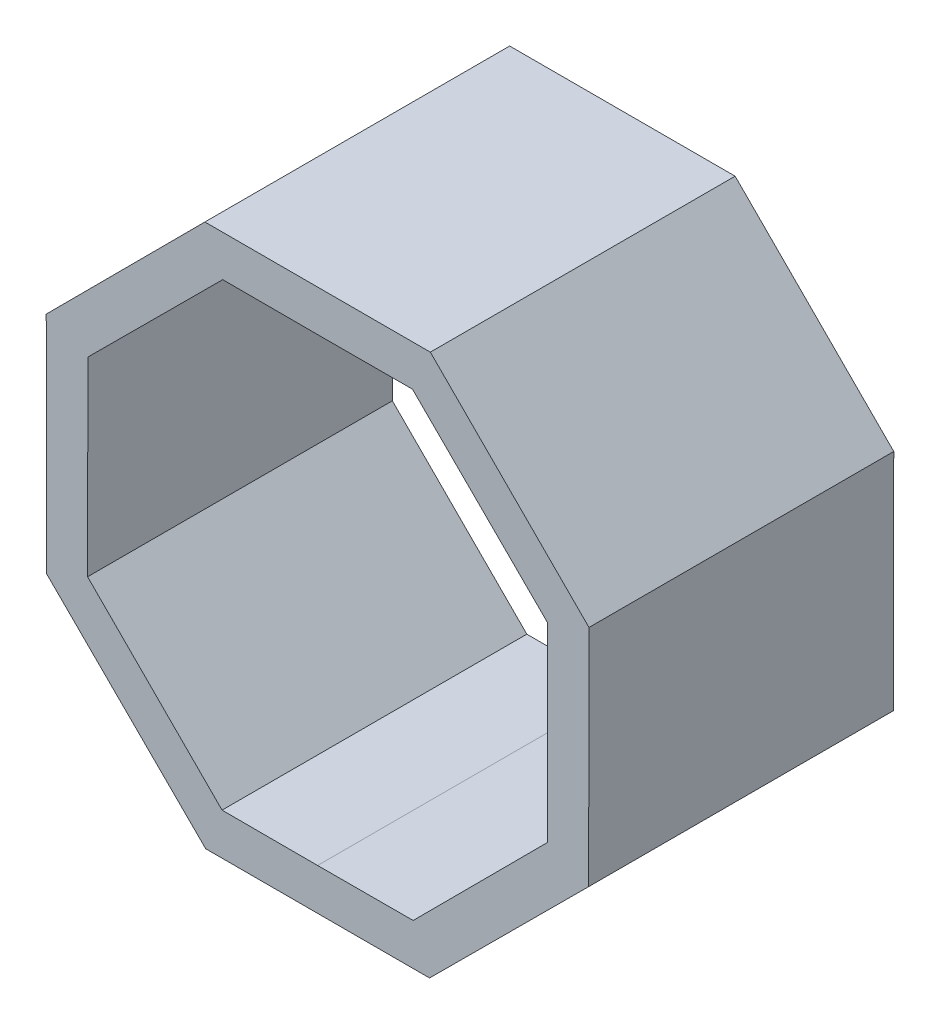
SolidWorks part; units mm, degrees
ref_plane "Front Plane" through (0, 0, 0) normal (0, 0, 1) x (1, 0, 0)
ref_plane "Top Plane" through (0, 0, 0) normal (0, 1, 0) x (1, 0, 0)
ref_plane "Right Plane" through (0, 0, 0) normal (1, 0, 0) x (0, 0, -1)
ref_plane "Plane1" through (0, 0, 11) normal (0, 0, 1) x (1, 0, 0)
sketch "Sketch1" plane through (0, 0, 11) normal (0, 0, 1) x (1, 0, 0)
  line L2 (4.334, -10.5063) -> (10.4937, -4.3645)
  line L3 (0, 8.9) -> (3.6735, 8.9054)
  line L4 (4.3645, 10.4937) -> (10.5063, 4.334)
  line L5 (3.6735, 8.9054) -> (8.8946, 3.6994)
  line L6 (8.8946, 3.6994) -> (8.9054, -3.6735)
  line L7 (8.9054, -3.6735) -> (3.6994, -8.8946)
  line L8 (3.6994, -8.8946) -> (0, -8.9)
  line L11 (-4.3645, 10.4937) -> (4.3645, 10.4937)
  line L12 (-4.334, -10.5063) -> (4.334, -10.5063)
  line L14 (0, 0) -> (0, 2.6737) construction
  line L15 (0, 0) -> (0, -12.0874) construction
  line L16 (0, 0) -> (0, 14.5338) construction
  line L17 (0, 8.9) -> (-3.6735, 8.9054)
  line L18 (-4.3645, 10.4937) -> (-10.5063, 4.334)
  line L19 (-3.6735, 8.9054) -> (-8.8946, 3.6994)
  line L20 (-8.8946, 3.6994) -> (-8.9054, -3.6735)
  line L21 (-4.334, -10.5063) -> (-10.4937, -4.3645)
  line L22 (-8.9054, -3.6735) -> (-3.6994, -8.8946)
  line L23 (-3.6994, -8.8946) -> (0, -8.9)
  line L24 (-10.4937, -4.3645) -> (-10.5063, 4.334)
  line L25 (10.4937, -4.3645) -> (10.5063, 4.334)
  point P5 (0, 10.4937)
  point P26 (0, -10.5063)
extrude "Boss-Extrude1" add sketch "Sketch1" against normal blind 9.8
sketch "Sketch2" plane through (0, 0, 1.2) normal (0, 0, -1) x (-1, 0, 0)
  line L245 (4.3645, 10.4937) -> (-4.3645, 10.4937)
  line L246 (10.5063, 4.334) -> (4.3645, 10.4937)
  line L247 (4.334, -10.5063) -> (10.4937, -4.3645)
  line L248 (-4.334, -10.5063) -> (4.334, -10.5063)
  line L249 (-10.4937, -4.3645) -> (-4.334, -10.5063)
  line L250 (-4.3645, 10.4937) -> (-10.5063, 4.334)
  circle A50 centre (0, 0) radius 3.95
  arc A54 (10.4937, -4.3645) -> (10.5063, 4.334) centre (10.2009, -0.0148) ccw
  arc A55 (-10.5063, 4.334) -> (-10.4937, -4.3645) centre (-10.2009, -0.0148) ccw
extrude "Boss-Extrude2" add sketch "Sketch2" along normal blind 1.2
sketch "Sketch3" plane through (0, -10.5063, 0) normal (0, -1, 0) x (1, 0, 0)
  line L1 (-18.5676, 1.2) -> (20.2971, 1.2)
  line L2 (-18.5676, 1.2) -> (-18.5676, 0)
  line L3 (-18.5676, 0) -> (20.2971, 0)
  line L4 (20.2971, 1.2) -> (20.2971, 0)
  dimension "D1" = 1.2
extrude "Cut-Extrude1" cut sketch "Sketch3" against normal through all
sketch "Sketch5" plane through (0, 0, 1.2) normal (0, 0, -1) x (-1, 0, 0)
  line L16 (-4.3645, 10.4937) -> (-10.5063, 4.334)
  line L17 (-10.5063, 4.334) -> (-10.4937, -4.3645)
  line L18 (-10.4937, -4.3645) -> (-4.334, -10.5063)
  line L19 (-4.334, -10.5063) -> (4.334, -10.5063)
  line L20 (4.334, -10.5063) -> (10.4937, -4.3645)
  line L21 (10.4937, -4.3645) -> (10.5063, 4.334)
  line L22 (10.5063, 4.334) -> (4.3645, 10.4937)
  line L23 (4.3645, 10.4937) -> (-4.3645, 10.4937)
  line L24 (-4.3645, 10.4937) -> (-10.5063, 4.334)
  line L25 (-10.5063, 4.334) -> (-10.4937, -4.3645)
  line L26 (-10.4937, -4.3645) -> (-4.334, -10.5063)
  line L27 (-4.334, -10.5063) -> (4.334, -10.5063)
  line L28 (4.334, -10.5063) -> (10.4937, -4.3645)
  line L29 (10.4937, -4.3645) -> (10.5063, 4.334)
  line L30 (10.5063, 4.334) -> (4.3645, 10.4937)
  line L31 (4.3645, 10.4937) -> (-4.3645, 10.4937)
  line L88 (-8.8946, 3.6994) -> (-8.9054, -3.6735)
  line L89 (-8.9054, -3.6735) -> (-3.6994, -8.8946)
  line L90 (-3.6994, -8.8946) -> (0, -8.9)
  line L91 (0, -8.9) -> (3.6994, -8.8946)
  line L92 (3.6994, -8.8946) -> (8.9054, -3.6735)
  line L93 (8.9054, -3.6735) -> (8.8946, 3.6994)
  line L94 (8.8946, 3.6994) -> (3.6735, 8.9054)
  line L95 (3.6735, 8.9054) -> (0, 8.9)
  line L96 (0, 8.9) -> (-3.6735, 8.9054)
  line L97 (-3.6735, 8.9054) -> (-8.8946, 3.6994)
  line L98 (-8.8946, 3.6994) -> (-8.9054, -3.6735)
  line L99 (-8.9054, -3.6735) -> (-3.6994, -8.8946)
  line L100 (-3.6994, -8.8946) -> (0, -8.9)
  line L101 (0, -8.9) -> (3.6994, -8.8946)
  line L102 (3.6994, -8.8946) -> (8.9054, -3.6735)
  line L103 (8.9054, -3.6735) -> (8.8946, 3.6994)
  line L104 (8.8946, 3.6994) -> (3.6735, 8.9054)
  line L105 (3.6735, 8.9054) -> (0, 8.9)
  line L106 (0, 8.9) -> (-3.6735, 8.9054)
  line L107 (-3.6735, 8.9054) -> (-8.8946, 3.6994)
  dimension "D1" = 0
  dimension "D2" = 0
extrude "Boss-Extrude3" add sketch "Sketch5" along normal up to surface (2 mm away)
